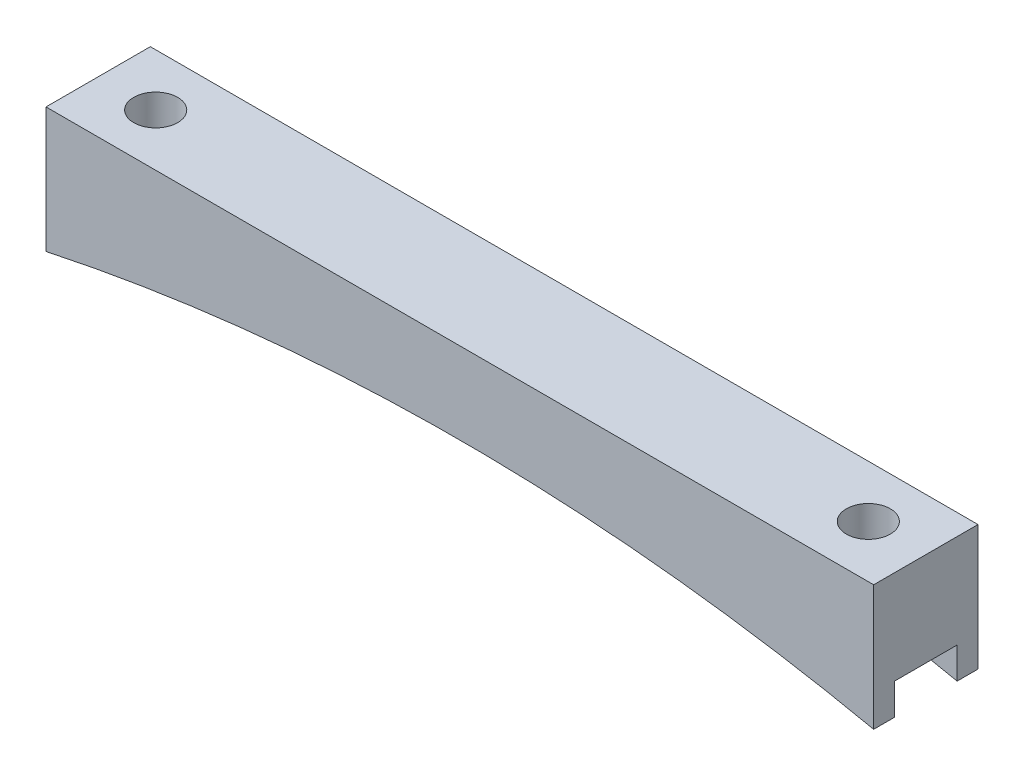
SolidWorks part; units mm, degrees
ref_plane "Front Plane" through (0, 0, 0) normal (0, 0, 1) x (1, 0, 0)
ref_plane "Top Plane" through (0, 0, 0) normal (0, 1, 0) x (1, 0, 0)
ref_plane "Right Plane" through (0, 0, 0) normal (1, 0, 0) x (0, 0, -1)
sketch "Sketch1" plane through (0, 0, 0) normal (0, 0, 1) x (1, 0, 0)
  line L0 (-50.37, 0) -> (50.37, 0)
  line L1 (-43.37, -2.54) -> (43.37, -2.54) construction
  line L2 (0, 0) -> (0, -4.6068) construction
  line L3 (50.37, 0) -> (50.37, -15.24)
  line L4 (-50.37, 0) -> (-50.37, -15.24)
  arc A0 (-50.37, -15.24) -> (50.37, -15.24) centre (0, -251.2242) cw
  point P4 (0, 0)
  point P9 (0, -2.54)
  dimension "D4" = 241.3
  dimension "D1" = 86.74
  dimension "D2" = 2.54
  dimension "D3" = 7
  dimension "D5" = 15.24
extrude "Boss-Extrude1" add sketch "Sketch1" along normal blind 12.7
sketch "Sketch2" plane through (0, 0, 0) normal (0, 1, 0) x (1, 0, 0)
  line L1 (-43.37, 0) -> (-43.37, -12.7) construction
  line L2 (-50.37, 0) -> (50.37, 0) construction
  line L3 (50.37, -12.7) -> (-50.37, -12.7) construction
  line L4 (43.37, 0) -> (43.37, -12.7) construction
  circle A0 centre (-43.37, -6.35) radius 2.675
  circle A1 centre (43.37, -6.35) radius 2.675
  circle A2 centre (-43.37, -6.35) radius 3 construction
  point P7 (-43.37, -6.35)
  dimension "D1" = 5.35
  dimension "D2" = 6
extrude "Cut-Extrude1" cut sketch "Sketch2" against normal through all
sketch "Sketch3" plane through (50.37, 0, 0) normal (1, 0, 0) x (0, 0, -1)
  line L0 (-12.7, -15.24) -> (0, -15.24) construction
  line L1 (-10.16, -15.24) -> (-2.54, -15.24)
  line L2 (-10.16, -15.24) -> (-10.16, -11.43)
  line L3 (-10.16, -11.43) -> (-2.54, -11.43)
  line L4 (-2.54, -15.24) -> (-2.54, -11.43)
  line L5 (-12.7, -15.24) -> (-12.7, 0) construction
  line L6 (0, -15.24) -> (0, 0) construction
  dimension "D1" = 2.54
  dimension "D2" = 2.54
  dimension "D3" = 3.81
extrude "Cut-Extrude2" cut sketch "Sketch3" against normal through all
